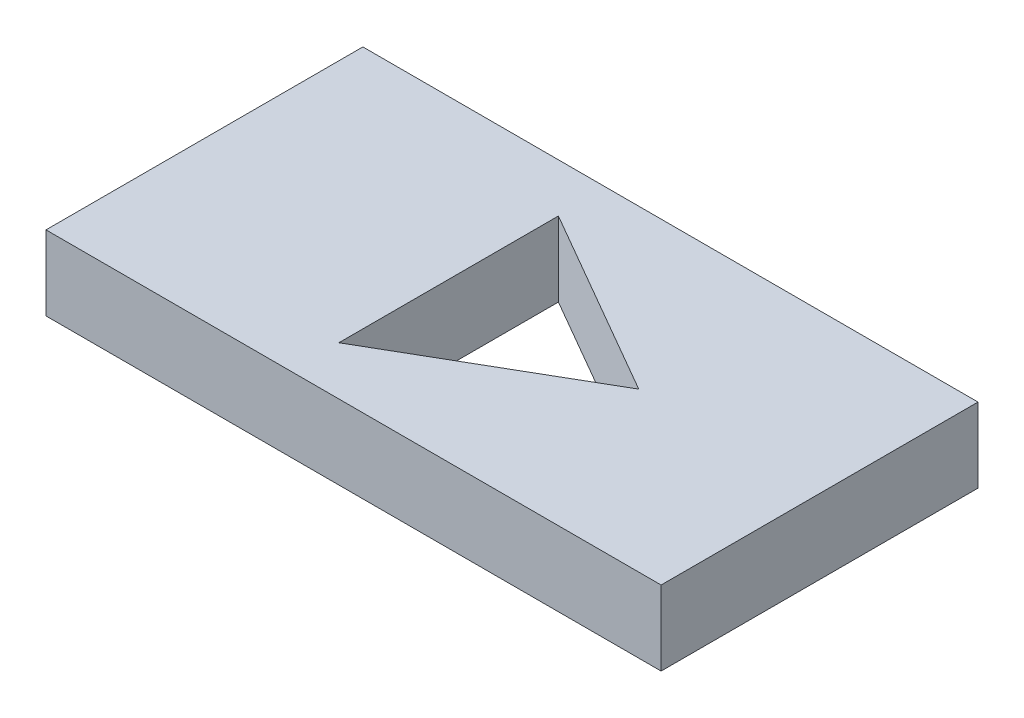
SolidWorks part; units mm, degrees
material "ABS"
ref_plane "Front" through (0, 0, 0) normal (0, 0, 1) x (1, 0, 0)
ref_plane "Top" through (0, 0, 0) normal (0, 1, 0) x (1, 0, 0)
ref_plane "Right" through (0, 0, 0) normal (1, 0, 0) x (0, 0, -1)
sketch "Sketch1" plane through (0, 0, 0) normal (0, 1, 0) x (1, 0, 0)
  line L0 (104.775, -53.975) -> (104.775, 53.975)
  line L1 (104.775, 53.975) -> (-104.775, 53.975)
  line L2 (-104.775, 53.975) -> (-104.775, -53.975)
  line L3 (-104.775, -53.975) -> (104.775, -53.975)
  line L4 (-21.59, 37.395) -> (-21.59, -37.395)
  line L5 (-21.59, -37.395) -> (43.18, 0)
  line L6 (43.18, 0) -> (-21.59, 37.395)
  line L7 (-104.775, 0) -> (104.775, 0) construction
  circle A0 centre (0, 0) radius 21.59 construction
  dimension "D3" = 43.18
  dimension "D1" = 209.55
  dimension "D2" = 107.95
extrude "Boss-Extrude1" add sketch "Sketch1" along normal blind 25.4
